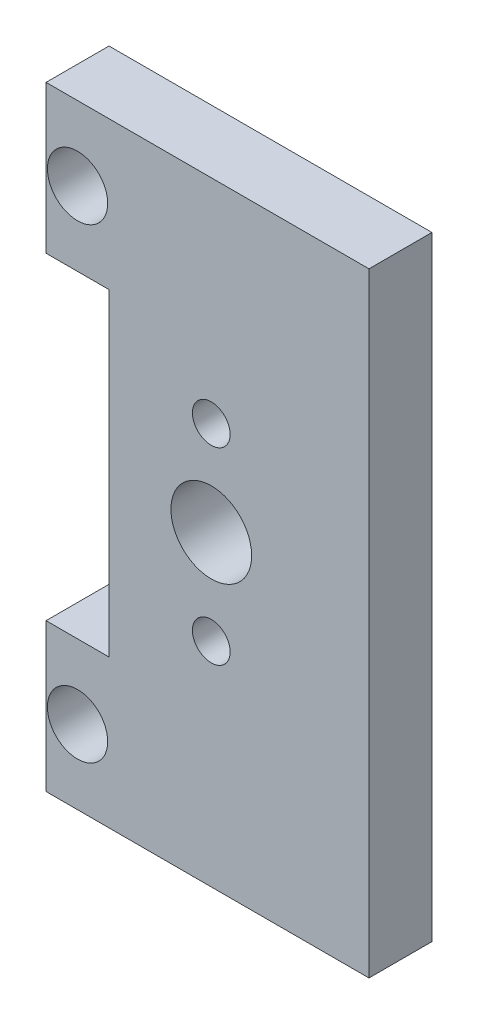
SolidWorks part; units mm, degrees
ref_plane "Front Plane" through (0, 0, 0) normal (0, 0, 1) x (1, 0, 0)
ref_plane "Top Plane" through (0, 0, 0) normal (0, 1, 0) x (1, 0, 0)
ref_plane "Right Plane" through (0, 0, 0) normal (1, 0, 0) x (0, 0, -1)
sketch "Sketch2" plane through (0, 0, 0) normal (0, 0, 1) x (1, 0, 0)
  line L0 (15.24, 14.4925) -> (0, 14.4925) construction
  line L1 (0, 0) -> (15.24, 0)
  line L2 (0, 0) -> (0, 28.985)
  line L5 (0, 28.985) -> (15.24, 28.985)
  line L6 (15.24, 0) -> (15.24, 28.985)
  line L7 (0, 6.985) -> (2.9718, 6.985)
  line L8 (0, 6.985) -> (0, 22)
  line L9 (0, 22) -> (2.9718, 22)
  line L10 (2.9718, 6.985) -> (2.9718, 22)
  circle A0 centre (1.4859, 25.4925) radius 1.4224
  circle A2 centre (1.4859, 3.4925) radius 1.4224
  circle A3 centre (7.7978, 14.4925) radius 1.905
  circle A4 centre (7.7978, 10.0475) radius 0.889
  circle A5 centre (7.7978, 18.9375) radius 0.889
  dimension "D3" = 6.985
  dimension "D7" = 1.4859
  dimension "D6" = 2.8448
  dimension "D9" = 3.81
  dimension "D11" = 1.778
  dimension "D1" = 2.9718
  dimension "D2" = 6.985
  dimension "D4" = 15.24
  dimension "D5" = 15.015
  dimension "D8" = 3.4925
  dimension "D10" = 4.826
  dimension "D12" = 4.445
extrude "Boss-Extrude1" add sketch "Sketch2" along normal blind 2.9718 contours L0 L6 L5 L2 L9 L10 A0 | L6 L0 L10 L7 L2 L1 A2
